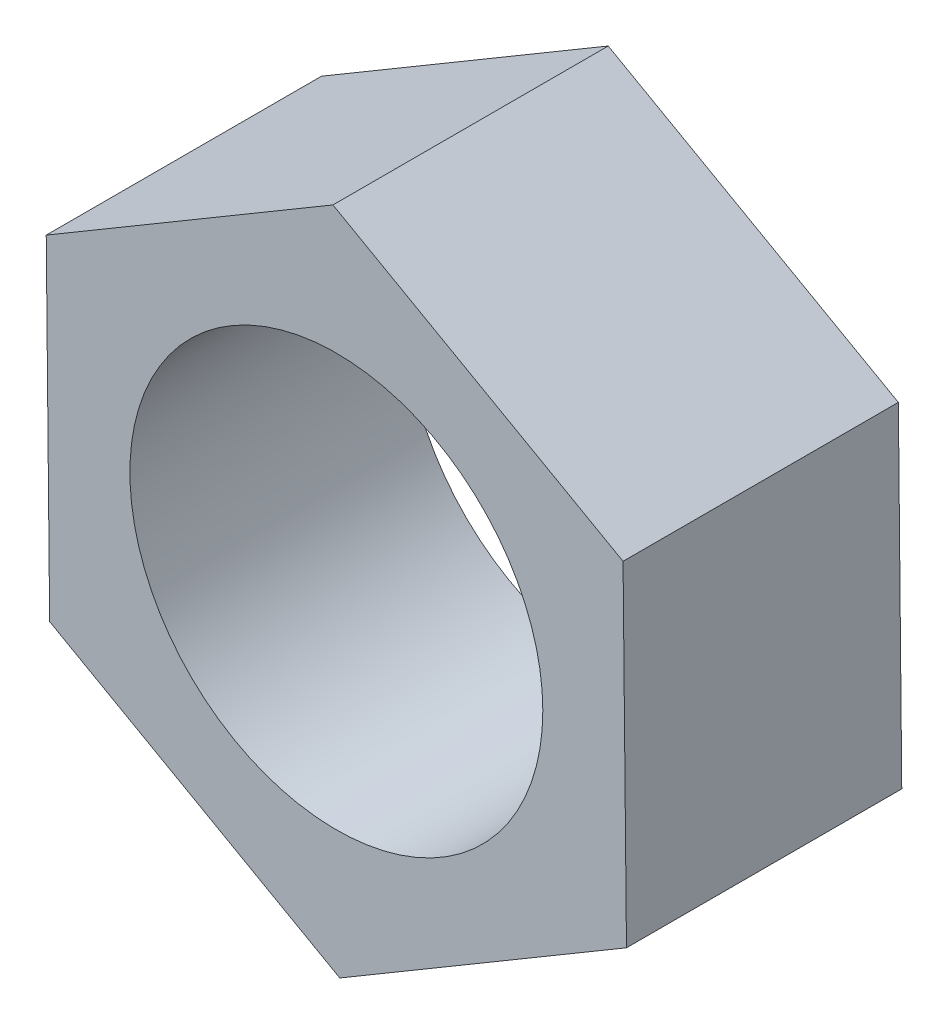
SolidWorks part; units mm, degrees
ref_plane "前视基准面" through (0, 0, 0) normal (0, 0, 1) x (1, 0, 0)
ref_plane "上视基准面" through (0, 0, 0) normal (0, 1, 0) x (1, 0, 0)
ref_plane "右视基准面" through (0, 0, 0) normal (1, 0, 0) x (0, 0, -1)
sketch "草图1" plane through (0, 0, 0) normal (0, 0, 1) x (1, 0, 0)
  line L1 (2.0829, 1.2313) -> (-0.0249, 2.4195)
  line L2 (-0.0249, 2.4195) -> (-2.1078, 1.1882)
  line L3 (-2.1078, 1.1882) -> (-2.0829, -1.2313)
  line L4 (-2.0829, -1.2313) -> (0.0249, -2.4195)
  line L5 (0.0249, -2.4195) -> (2.1078, -1.1882)
  line L6 (2.1078, -1.1882) -> (2.0829, 1.2313)
  circle A0 centre (0, 0) radius 1.5
  circle A1 centre (0, 0) radius 2.0955 construction
  dimension "D1" = 3
extrude "凸台-拉伸1" add sketch "草图1" along normal blind 2
